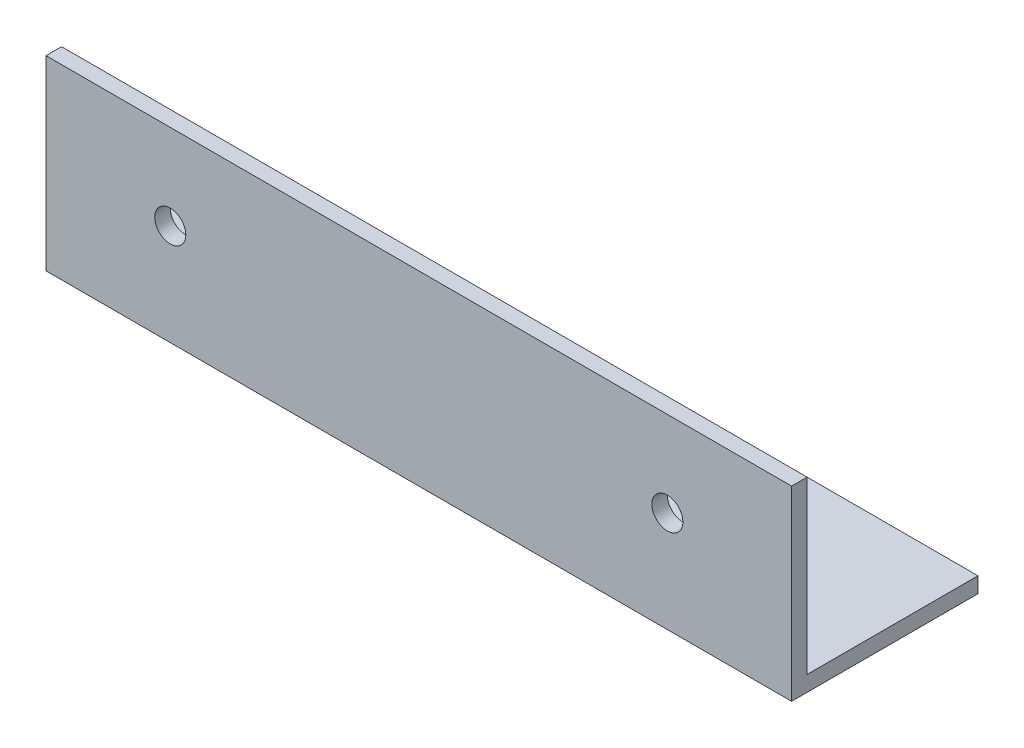
SolidWorks part; units mm, degrees
material "6063-O"
ref_plane "Front Plane" through (0, 0, 0) normal (0, 0, 1) x (1, 0, 0)
ref_plane "Top Plane" through (0, 0, 0) normal (0, 1, 0) x (1, 0, 0)
ref_plane "Right Plane" through (0, 0, 0) normal (1, 0, 0) x (0, 0, -1)
sketch "Sketch1" plane through (0, 0, 0) normal (1, 0, 0) x (0, 0, -1)
  line L0 (0, 0) -> (0, 38.1)
  line L1 (0, 38.1) -> (3.175, 38.1)
  line L2 (3.175, 38.1) -> (3.175, 3.175)
  line L3 (3.175, 3.175) -> (38.1, 3.175)
  line L4 (38.1, 3.175) -> (38.1, 0)
  line L5 (38.1, 0) -> (0, 0)
  dimension "D1" = 3.175
  dimension "D2" = 3.175
  dimension "D3" = 38.1
  dimension "D4" = 38.1
extrude "Boss-Extrude1" add sketch "Sketch1" along normal blind 152.4
sketch "Sketch5" plane through (0, 0, -3.175) normal (0, 0, -1) x (-1, 0, 0)
  line L0 (-76.2, 38.1) -> (-76.2, 3.175) construction
  line L1 (-152.4, 38.1) -> (0, 38.1) construction
  line L2 (-152.4, 3.175) -> (0, 3.175) construction
  line L3 (-76.2, 20.6375) -> (-127, 20.6375) construction
  circle A0 centre (-127, 20.6375) radius 3.175
  circle A1 centre (-25.4, 20.6375) radius 3.175
  dimension "D1" = 6.35
  dimension "D2" = 50.8
extrude "Cut-Extrude3" cut sketch "Sketch5" against normal through all
sketch "Sketch6" plane through (0, 3.175, 0) normal (0, 1, 0) x (1, 0, 0)
  line L0 (76.2, 38.1) -> (76.2, 3.175) construction
  line L1 (152.4, 38.1) -> (0, 38.1) construction
  line L2 (152.4, 3.175) -> (0, 3.175) construction
  line L3 (76.2, 20.6375) -> (25.4, 20.6375) construction
  circle A0 centre (25.4, 20.6375) radius 3.175
  circle A1 centre (127, 20.6375) radius 3.175
  dimension "D1" = 6.35
  dimension "D2" = 50.8
extrude "Cut-Extrude4" cut sketch "Sketch6" against normal through all
